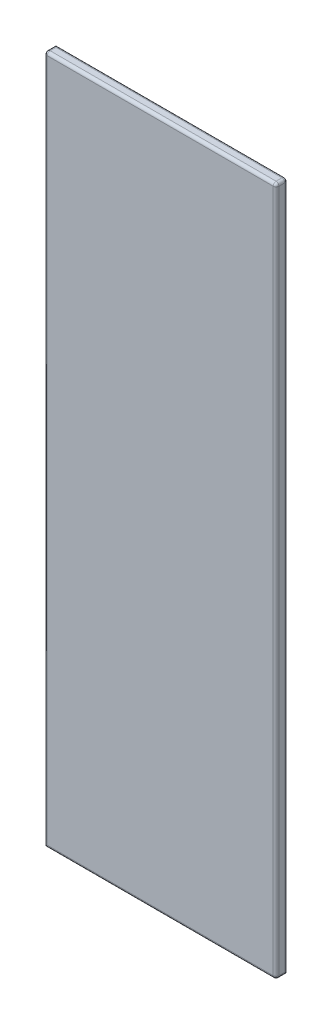
SolidWorks part; units mm, degrees
material "1060 Alloy"
ref_plane "Front Plane" through (0, 0, 0) normal (0, 0, 1) x (1, 0, 0)
ref_plane "Top Plane" through (0, 0, 0) normal (0, 1, 0) x (1, 0, 0)
ref_plane "Right Plane" through (0, 0, 0) normal (1, 0, 0) x (0, 0, -1)
sketch "Sketch1" plane through (0, 0, 0) normal (0, 0, 1) x (1, 0, 0)
  line L1 (-200, 595) -> (200, 595)
  line L2 (-200, 595) -> (-200, -595)
  line L3 (-200, -595) -> (200, -595)
  line L4 (200, 595) -> (200, -595)
  line L5 (-200, 595) -> (200, -595) construction
  line L6 (-200, -595) -> (200, 595) construction
  point P0 (0, 0)
  dimension "D1" = 400
  dimension "D2" = 1190
extrude "Boss-Extrude1" add sketch "Sketch1" along normal blind 20
fillet "Fillet1" radius 5 9 edges at (200, 0, 0) (0, 595, 0) (200, 0, 20) (0, 595, 20) (-200, 0, 20) (0, -595, 20) (200, -595, 10) (-200, 595, 10) (200, 595, 10)
